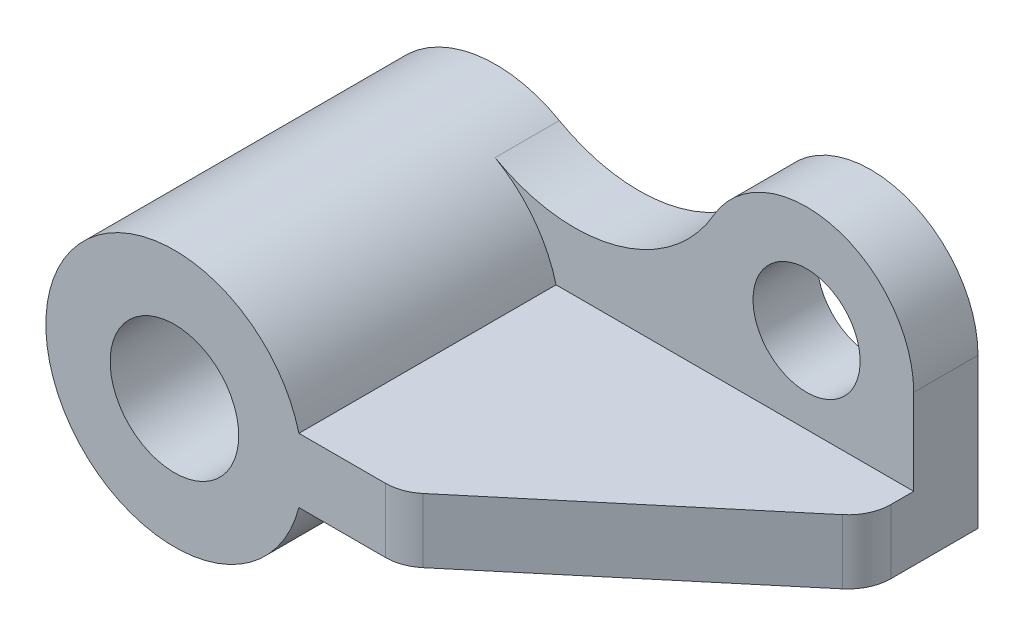
SolidWorks part; units mm, degrees
material "Plain Carbon Steel"
ref_plane "Front Plane" through (0, 0, 0) normal (0, 0, 1) x (1, 0, 0)
ref_plane "Top Plane" through (0, 0, 0) normal (0, 1, 0) x (1, 0, 0)
ref_plane "Right Plane" through (0, 0, 0) normal (1, 0, 0) x (0, 0, -1)
sketch "Sketch1" plane through (0, 0, 0) normal (0, 0, 1) x (1, 0, 0)
  line L0 (0, 0) -> (182.8678, 0) construction
  line L1 (58.0948, 15) -> (225, 15)
  line L3 (58.0948, -15) -> (225, -15)
  line L4 (225, 15) -> (225, -15)
  arc A0 (58.0948, 15) -> (58.0948, -15) centre (0, 0) ccw
  circle A1 centre (0, 0) radius 30
  dimension "D1" = 60
  dimension "D2" = 120
  dimension "D3" = 225
  dimension "D4" = 30
extrude "Boss-Extrude1" add sketch "Sketch1" along normal mid plane 150
sketch "Sketch2" plane through (0, 0, -75) normal (0, 0, -1) x (-1, 0, 0)
  line L0 (-225, 15) -> (-225, 55)
  line L1 (-225, 15) -> (-58.0948, 15) construction
  line L2 (-225, 15) -> (-58.0948, 15)
  arc A0 (-225, 55) -> (-131.6718, 79.9533) centre (-175, 55) cw
  arc A1 (-131.6718, 79.9533) -> (-29.6353, 52.1704) centre (-66.6795, 117.3833) ccw
  arc A2 (-58.0948, -15) -> (-58.0948, 15) centre (0, 0) ccw construction
  arc A3 (-29.6353, 52.1704) -> (-58.0948, 15) centre (0, 0) ccw
  circle A4 centre (-175, 55) radius 25
  dimension "D2" = 50
  dimension "D3" = 75
  dimension "D4" = 50
  dimension "D1" = 40
extrude "Boss-Extrude2" add sketch "Sketch2" against normal blind 30
sketch "Sketch3" plane through (0, 15, 0) normal (0, 1, 0) x (1, 0, 0)
  line L0 (225, 25) -> (105.8246, -75)
  line L1 (225, -75) -> (225, 45) construction
  line L2 (225, -75) -> (58.0948, -75) construction
  line L3 (105.8246, -75) -> (225, -75)
  line L4 (225, -75) -> (225, 25)
  line L6 (225, 75) -> (131.6718, 75) construction
  dimension "D1" = 50
  dimension "D2" = 130
extrude "Cut-Extrude1" cut sketch "Sketch3" against normal through all
fillet "Fillet1" radius 20 2 edges at (225, 0, -25) (105.8246, 0, 75)
